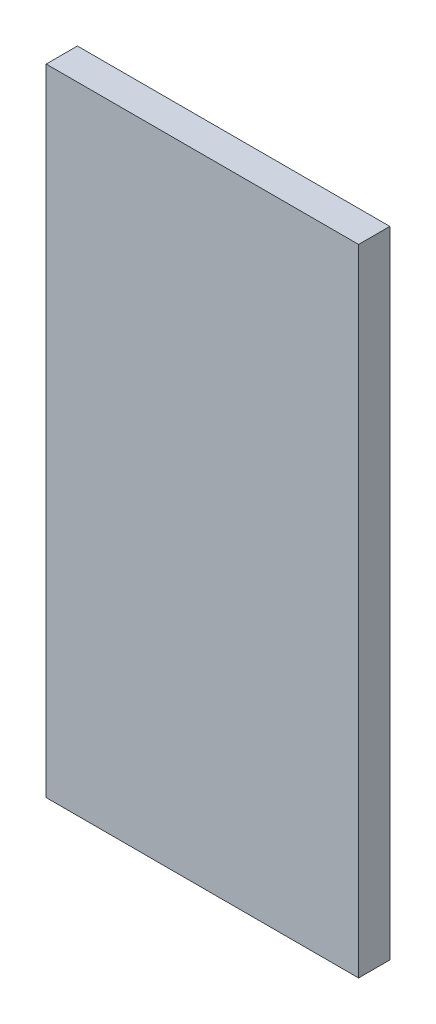
SolidWorks part; units mm, degrees
ref_plane "Front Plane" through (0, 0, 0) normal (0, 0, 1) x (1, 0, 0)
ref_plane "Top Plane" through (0, 0, 0) normal (0, 1, 0) x (1, 0, 0)
ref_plane "Right Plane" through (0, 0, 0) normal (1, 0, 0) x (0, 0, -1)
sketch "Model" plane through (0, 0, 0) normal (0, 0, 1) x (1, 0, 0)
  line L248 (-95.3504, 43.9908) -> (-95.3504, 104.9908)
  line L249 (-95.3504, 104.9908) -> (-125.3504, 104.9908)
  line L250 (-125.3504, 104.9908) -> (-125.3504, 43.9908)
  line L251 (-125.3504, 43.9908) -> (-95.3504, 43.9908)
  dimension "D1" = 30
  dimension "D2" = 61
extrude "Boss-Extrude1" add sketch "Model" along normal blind 3
